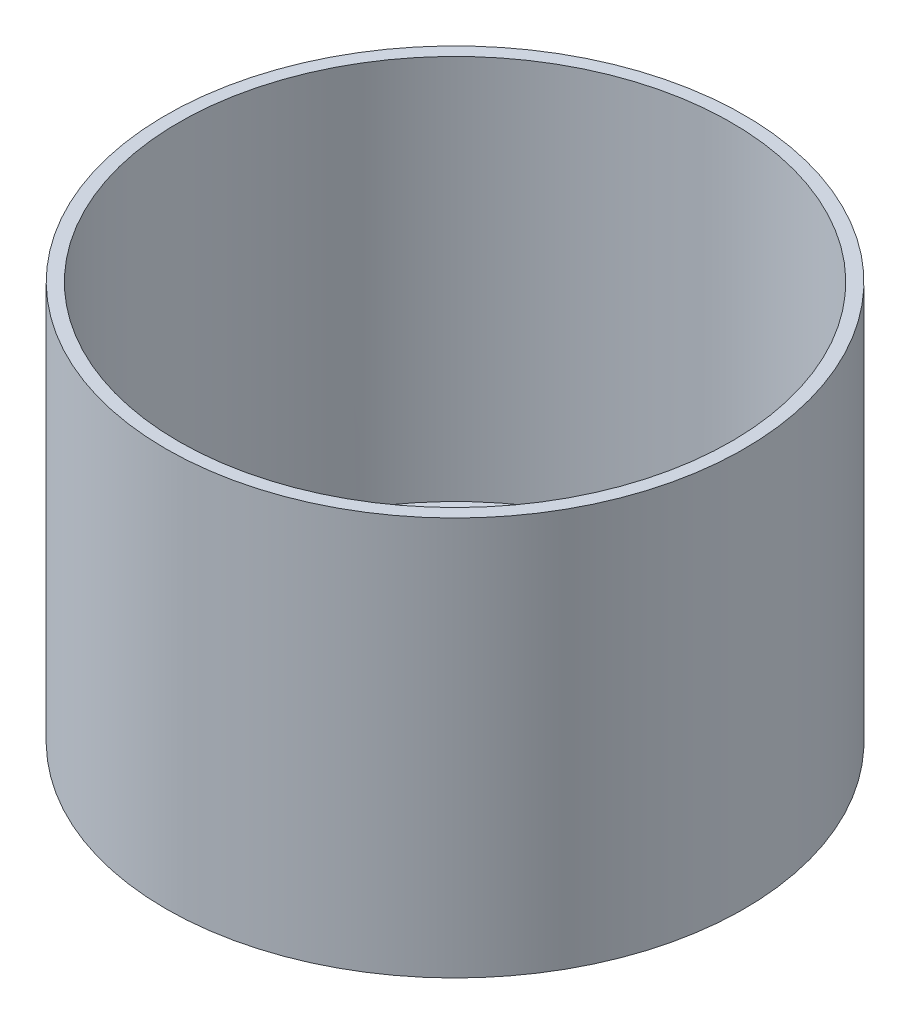
SolidWorks part; units mm, degrees
ref_plane "Front Plane" through (0, 0, 0) normal (0, 0, 1) x (1, 0, 0)
ref_plane "Top Plane" through (0, 0, 0) normal (0, 1, 0) x (1, 0, 0)
ref_plane "Right Plane" through (0, 0, 0) normal (1, 0, 0) x (0, 0, -1)
sketch "Sketch1" plane through (0, 0, 0) normal (0, 1, 0) x (1, 0, 0)
  circle A0 centre (16.5, 24.5) radius 45
  point P3 (0, 0)
extrude "Boss-Extrude1" add sketch "Sketch1" along normal blind 2
sketch "Sketch2" plane through (0, 2, 0) normal (0, 1, 0) x (1, 0, 0)
  circle A0 centre (16.5, 24.5) radius 43
  circle A1 centre (16.5, 24.5) radius 45
  point P4 (0, 0)
extrude "Boss-Extrude2" add sketch "Sketch2" along normal blind 60
sketch "Sketch4" plane through (0, 2, 0) normal (0, 1, 0) x (1, 0, 0)
  line L7 (13.693, -17.9436) -> (-2.3488, -12.5318)
  line L8 (-5.3558, 32.0029) -> (-5.3558, 27.2468) construction
  line L9 (31.2555, 6.7224) -> (21.3299, 3.8839) construction
  line L10 (16.4691, -7.5299) -> (11.3525, -5.8038)
  line L11 (31.2555, 6.7224) -> (16.1556, 12.3943) construction
  line L12 (18.3824, -4.2272) -> (16.1556, 12.3943) construction
  line L13 (18.3824, -4.2272) -> (31.2555, 6.7224) construction
  line L14 (16.1556, 12.3943) -> (21.3299, 3.8839) construction
  line L15 (18.3824, -4.2272) -> (21.3299, 3.8839) construction
  line L16 (16.6228, -5.7328) -> (13.7483, -4.7631)
  line L17 (13.119, -19.6448) -> (-2.7747, -14.283)
  line L19 (13.119, -19.6448) -> (-2.9227, -14.233) construction
  line L20 (17.0292, -5.8699) -> (11.9125, -4.1438) construction
  circle A11 centre (24.7606, 35.122) radius 0.7791 construction
  circle A13 centre (31.2555, 6.7224) radius 0.8 construction
  circle A14 centre (18.3824, -4.2272) radius 0.8214 construction
  arc A15 (13.119, -19.6448) -> (16.6228, -5.7328) centre (15.4191, -12.8269) ccw
  arc A16 (13.693, -17.9436) -> (16.4691, -7.5299) centre (15.4191, -12.8269) ccw
  circle A19 centre (16.1556, 12.3943) radius 1.0096 construction
  arc A20 (11.3525, -5.8038) -> (-2.3488, -12.5318) centre (0, 0) ccw
  arc A21 (13.7483, -4.7631) -> (-2.7747, -14.283) centre (0, 0) ccw
  point P16 (3.1531, 9.1121)
  point P20 (-1.026, 21.7068)
  point P21 (11.1548, -5.7508)
  dimension "D1" = 16.93
  dimension "D2" = 16.13
  dimension "D3" = 5.4
  dimension "D6" = 9.96
  dimension "D4" = 16.77
  dimension "D5" = 16.9
  dimension "D7" = 8.63
extrude "Boss-Extrude3" add sketch "Sketch4" along normal blind 20
